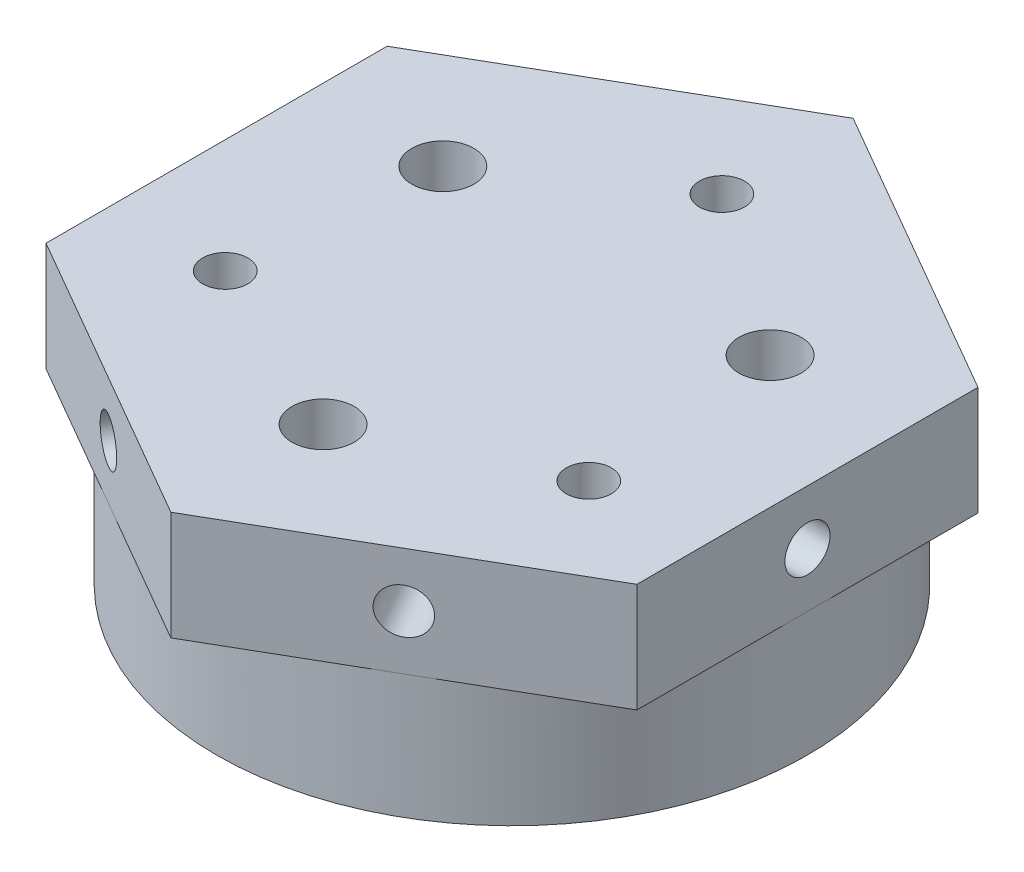
SolidWorks part; units mm, degrees
ref_plane "前视基准面" through (0, 0, 0) normal (0, 0, 1) x (1, 0, 0)
ref_plane "上视基准面" through (0, 0, 0) normal (0, 1, 0) x (1, 0, 0)
ref_plane "右视基准面" through (0, 0, 0) normal (1, 0, 0) x (0, 0, -1)
sketch "草图1" plane through (0, 0, 0) normal (0, 1, 0) x (1, 0, 0)
  line L0 (0, 0) -> (0, 33.3478) construction
  line L1 (0, 0) -> (11.2563, 0) construction
  line L2 (-11.6913, -6.75) -> (0, 0) construction
  line L3 (0, 0) -> (11.6913, -6.75) construction
  line L4 (0, 0) -> (-10.5222, 6.075) construction
  line L5 (10.5222, 6.075) -> (0, 0) construction
  circle A0 centre (0, 0) radius 19
  circle A1 centre (0, 13.5) radius 1.45
  circle A2 centre (0, 0) radius 13.5 construction
  circle A3 centre (-11.6913, -6.75) radius 1.45
  circle A4 centre (11.6913, -6.75) radius 1.45
  circle A5 centre (0, 0) radius 12.15 construction
  circle A6 centre (-10.5222, 6.075) radius 2
  circle A7 centre (0, -12.15) radius 2
  circle A8 centre (10.5222, 6.075) radius 2
  dimension "D1" = 38
  dimension "D2" = 27
  dimension "D3" = 2.9
  dimension "D6" = 24.3
  dimension "D8" = 4
  dimension "D4" = 120
  dimension "D5" = 120
  dimension "D7" = 60
  dimension "D9" = 60
extrude "凸台-拉伸1" add sketch "草图1" along normal blind 15
sketch "草图2" plane through (0, 15, 0) normal (0, 1, 0) x (1, 0, 0)
  line L0 (0, 21.9393) -> (0, 0) construction
  line L1 (0, 21.9393) -> (-19, 10.9697)
  line L2 (-19, 10.9697) -> (-19, -10.9697)
  line L3 (-19, -10.9697) -> (0, -21.9393)
  line L4 (0, -21.9393) -> (19, -10.9697)
  line L5 (19, -10.9697) -> (19, 10.9697)
  line L6 (19, 10.9697) -> (0, 21.9393)
  circle A0 centre (0, 0) radius 19 construction
  circle A1 centre (0, 13.5) radius 1.45
  circle A2 centre (0, 13.5) radius 1.45 construction
  circle A3 centre (-10.5222, 6.075) radius 2
  circle A4 centre (-10.5222, 6.075) radius 2 construction
  circle A5 centre (10.5222, 6.075) radius 2
  circle A6 centre (10.5222, 6.075) radius 2 construction
  circle A7 centre (-11.6913, -6.75) radius 1.45
  circle A8 centre (-11.6913, -6.75) radius 1.45 construction
  circle A9 centre (0, -12.15) radius 2
  circle A10 centre (0, -12.15) radius 2 construction
  circle A11 centre (11.6913, -6.75) radius 1.45
  circle A12 centre (11.6913, -6.75) radius 1.45 construction
  dimension "D1" = 38
extrude "凸台-拉伸2" add sketch "草图2" against normal blind 7
sketch "草图3" plane through (9.5, 0, 16.4545) normal (0.5, 0, 0.866) x (0.866, 0, -0.5)
  line L1 (0, 15) -> (0, 8) construction
  line L2 (-10.9697, 15) -> (10.9697, 15) construction
  circle A1 centre (0, 11.5) radius 1.45
  dimension "D1" = 2.9
extrude "切除-拉伸1" cut sketch "草图3" against normal blind 8
sketch "草图4" plane through (-9.5, 0, 16.4545) normal (-0.5, 0, 0.866) x (0.866, 0, 0.5)
  line L0 (0, 8) -> (0, 15) construction
  line L1 (-10.9697, 15) -> (10.9697, 15) construction
  circle A0 centre (0, 11.5) radius 1.45
  dimension "D1" = 2.9
extrude "切除-拉伸2" cut sketch "草图4" against normal blind 8
sketch "草图5" plane through (-19, 0, 0) normal (-1, 0, 0) x (0, 0, 1)
  line L0 (0, 8) -> (0, 15) construction
  line L1 (-10.9697, 15) -> (10.9697, 15) construction
  circle A0 centre (0, 11.5) radius 1.45
  dimension "D1" = 2.9
extrude "切除-拉伸3" cut sketch "草图5" against normal blind 8
sketch "草图6" plane through (19, 0, 0) normal (1, 0, 0) x (0, 0, -1)
  line L0 (0, 15) -> (0, 8) construction
  line L1 (-10.9697, 15) -> (10.9697, 15) construction
  circle A0 centre (0, 11.5) radius 1.45
  dimension "D1" = 2.9
extrude "切除-拉伸4" cut sketch "草图6" against normal blind 8
sketch "草图7" plane through (9.5, 0, -16.4545) normal (0.5, 0, -0.866) x (-0.866, 0, -0.5)
  line L0 (0, 15) -> (0, 8) construction
  line L1 (-10.9697, 15) -> (10.9697, 15) construction
  circle A0 centre (0, 11.5) radius 1.45
  dimension "D1" = 2.9
extrude "切除-拉伸5" cut sketch "草图7" against normal blind 8
